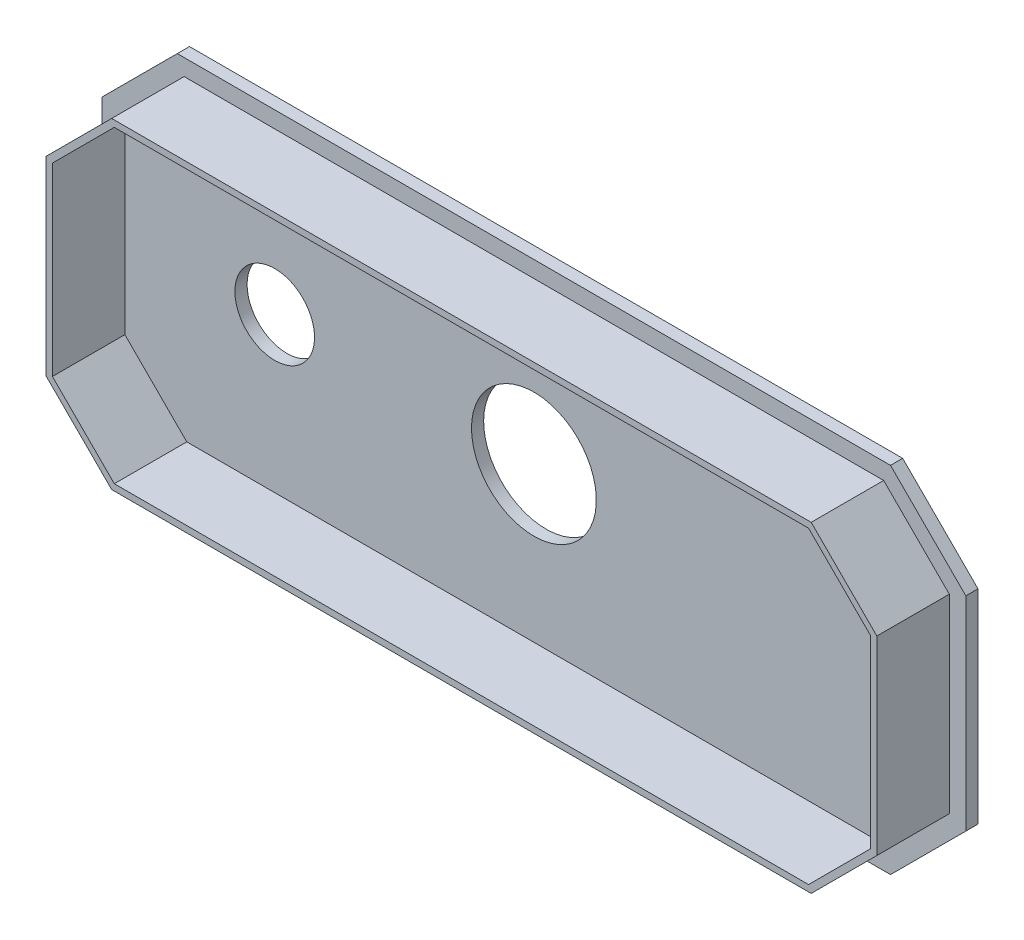
SolidWorks part; units mm, degrees
ref_plane "Front Plane" through (0, 0, 0) normal (0, 0, 1) x (1, 0, 0)
ref_plane "Top Plane" through (0, 0, 0) normal (0, 1, 0) x (1, 0, 0)
ref_plane "Right Plane" through (0, 0, 0) normal (1, 0, 0) x (0, 0, -1)
sketch "Sketch1" plane through (0, 0, 0) normal (0, 0, 1) x (1, 0, 0)
  line L1 (-28.3845, -11.6459) -> (28.3845, -11.6459)
  line L2 (-28.3845, -11.6459) -> (-28.3845, 11.6459)
  line L3 (-28.3845, 11.6459) -> (28.3845, 11.6459)
  line L4 (28.3845, -11.6459) -> (28.3845, 11.6459)
  line L5 (-28.3845, -11.6459) -> (28.3845, 11.6459) construction
  line L6 (-28.3845, 11.6459) -> (28.3845, -11.6459) construction
  point P0 (0, 0)
  dimension "D1" = 56.769
  dimension "D2" = 23.2918
extrude "Boss-Extrude1" add sketch "Sketch1" along normal blind 0.8
sketch "Sketch2" plane through (0, 0, 0.8) normal (0, 0, 1) x (1, 0, 0)
  line L0 (-28.3845, -6.6962) -> (-23.4348, -11.6459)
  line L1 (-28.3845, 11.6459) -> (-28.3845, -11.6459) construction
  line L2 (-28.3845, 6.6962) -> (-23.4348, 11.6459)
  line L3 (28.3845, 11.6459) -> (-28.3845, 11.6459) construction
  line L4 (-23.4348, 11.6459) -> (-28.3845, 11.6459)
  line L5 (-28.3845, 11.6459) -> (-28.3845, 6.6962)
  line L6 (-28.3845, -11.6459) -> (28.3845, -11.6459) construction
  line L7 (-23.4348, -11.6459) -> (-28.3845, -11.6459)
  line L8 (-28.3845, -11.6459) -> (-28.3845, -6.6962)
  line L9 (23.4348, -11.6459) -> (28.3845, -6.6962)
  line L10 (28.3845, -11.6459) -> (28.3845, 11.6459) construction
  line L11 (28.3845, -6.6962) -> (28.3845, -11.6459)
  line L12 (28.3845, -11.6459) -> (23.4348, -11.6459)
  line L13 (23.4348, 11.6459) -> (28.3845, 6.6962)
  line L14 (28.3845, 6.6962) -> (28.3845, 11.6459)
  line L15 (28.3845, 11.6459) -> (23.4348, 11.6459)
  dimension "D1" = 7
  dimension "D2" = 7
  dimension "D3" = 7
  dimension "D4" = 7
  dimension "D5" = 45
  dimension "D6" = 45
  dimension "D7" = 45
  dimension "D8" = 45
extrude "Cut-Extrude1" cut sketch "Sketch2" against normal through all
sketch "Sketch3" plane through (0, 0, 0.8) normal (0, 0, 1) x (1, 0, 0)
  line L0 (22.9854, 10.5611) -> (-22.9854, 10.5611)
  line L1 (-22.9854, 10.5611) -> (-27.2997, 6.2468)
  line L2 (-27.2997, 6.2468) -> (-27.2997, -6.2468)
  line L3 (-27.2997, -6.2468) -> (-22.9854, -10.5611)
  line L4 (-22.9854, -10.5611) -> (22.9854, -10.5611)
  line L5 (22.9854, -10.5611) -> (27.2997, -6.2468)
  line L6 (27.2997, -6.2468) -> (27.2997, 6.2468)
  line L7 (27.2997, 6.2468) -> (22.9854, 10.5611)
  line L48 (-22.8114, 10.1411) -> (-26.8797, 6.0728)
  line L49 (-26.8797, 6.0728) -> (-26.8797, -6.0728)
  line L50 (-26.8797, -6.0728) -> (-22.8114, -10.1411)
  line L51 (-22.8114, -10.1411) -> (22.8114, -10.1411)
  line L52 (22.8114, -10.1411) -> (26.8797, -6.0728)
  line L53 (26.8797, -6.0728) -> (26.8797, 6.0728)
  line L54 (26.8797, 6.0728) -> (22.8114, 10.1411)
  line L55 (22.8114, 10.1411) -> (-22.8114, 10.1411)
  line L56 (-22.8114, 10.1411) -> (-26.8797, 6.0728)
  line L57 (-26.8797, 6.0728) -> (-26.8797, -6.0728)
  line L58 (-26.8797, -6.0728) -> (-22.8114, -10.1411)
  line L59 (-22.8114, -10.1411) -> (22.8114, -10.1411)
  line L60 (22.8114, -10.1411) -> (26.8797, -6.0728)
  line L61 (26.8797, -6.0728) -> (26.8797, 6.0728)
  line L62 (26.8797, 6.0728) -> (22.8114, 10.1411)
  line L63 (22.8114, 10.1411) -> (-22.8114, 10.1411)
  dimension "D1" = 1.5048
  dimension "D2" = 0.42
extrude "Boss-Extrude2" add sketch "Sketch3" along normal blind 4.7625
sketch "Sketch4" plane through (0, 0, 0) normal (0, 0, -1) x (-1, 0, 0)
  line L0 (17.0307, 0) -> (0, 0) construction
  line L1 (28.3845, 6.6962) -> (28.3845, -6.6962) construction
  circle A0 centre (17.0307, 0) radius 2.6162
  dimension "D1" = 5.2324
  dimension "D2" = 11.3538
extrude "Cut-Extrude2" cut sketch "Sketch4" against normal blind 2.54
sketch "Sketch5" plane through (0, 0, 0) normal (0, 0, -1) x (-1, 0, 0)
  circle A0 centre (0, 0) radius 4.1021
  dimension "D1" = 8.2042
extrude "Cut-Extrude3" cut sketch "Sketch5" against normal blind 2.54
